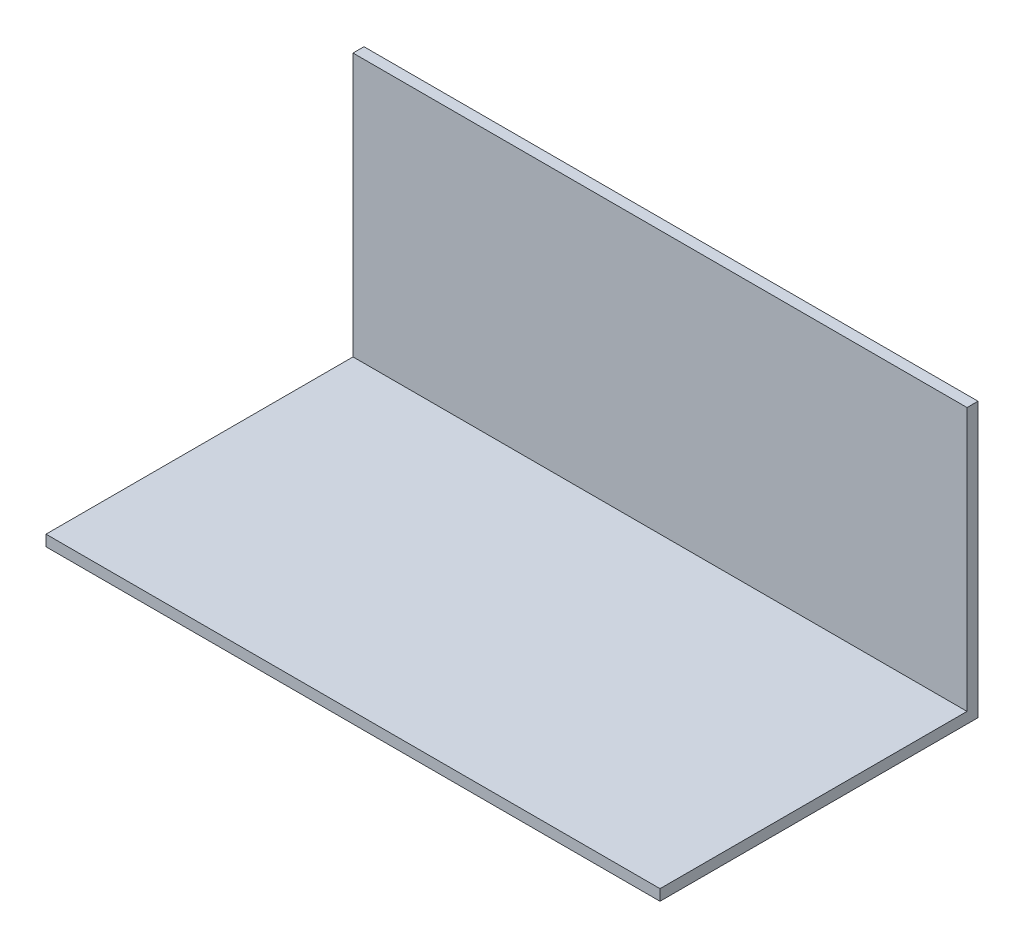
SolidWorks part; units mm, degrees
ref_plane "Front Plane" through (0, 0, 0) normal (0, 0, 1) x (1, 0, 0)
ref_plane "Top Plane" through (0, 0, 0) normal (0, 1, 0) x (1, 0, 0)
ref_plane "Right Plane" through (0, 0, 0) normal (1, 0, 0) x (0, 0, -1)
sketch "Sketch1" plane through (0, 0, 0) normal (0, 1, 0) x (1, 0, 0)
  line L1 (0, 0) -> (355.6, 0)
  line L2 (0, 0) -> (0, 184.15)
  line L3 (0, 184.15) -> (355.6, 184.15)
  line L4 (355.6, 0) -> (355.6, 184.15)
  dimension "D1" = 355.6
  dimension "D2" = 184.15
extrude "Boss-Extrude1" add sketch "Sketch1" along normal blind 6.35
sketch "Sketch2" plane through (0, 6.35, 0) normal (0, 1, 0) x (1, 0, 0)
  line L0 (0, 184.15) -> (0, 0) construction
  line L1 (0, 177.8) -> (355.6, 177.8)
  line L2 (0, 177.8) -> (0, 184.15)
  line L3 (0, 184.15) -> (355.6, 184.15)
  line L4 (355.6, 177.8) -> (355.6, 184.15)
  line L5 (355.6, 0) -> (355.6, 184.15) construction
  line L6 (0, 0) -> (355.6, 0) construction
  dimension "D1" = 355.6
  dimension "D2" = 6.35
  dimension "D3" = 177.8
extrude "Boss-Extrude2" add sketch "Sketch2" along normal blind 152.4
